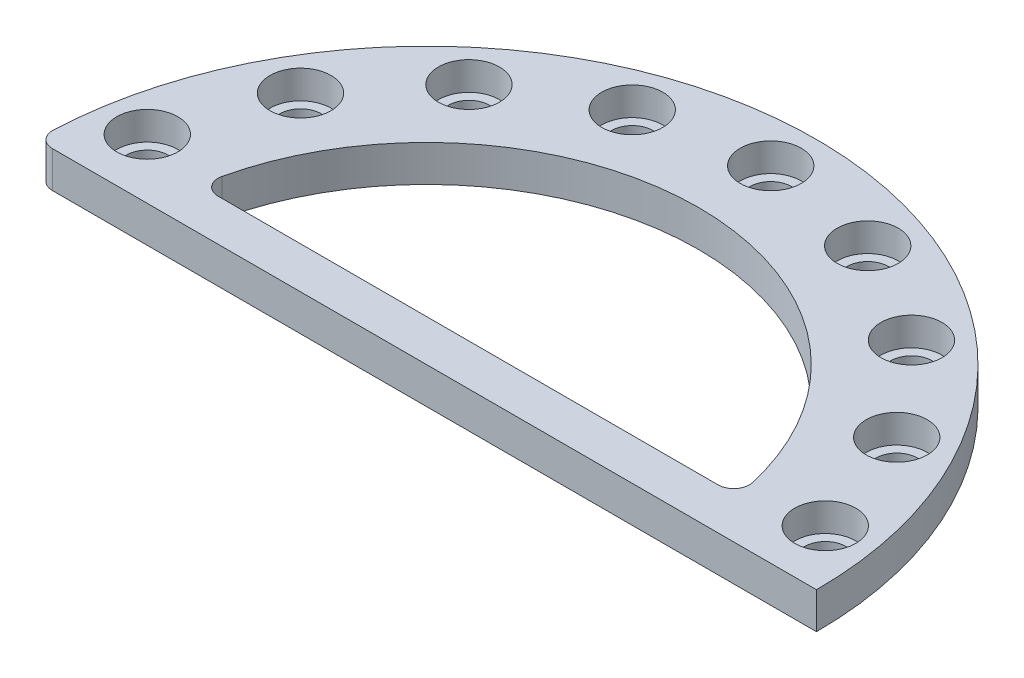
SolidWorks part; units mm, degrees
ref_plane "Front Plane" through (0, 0, 0) normal (0, 0, 1) x (1, 0, 0)
ref_plane "Top Plane" through (0, 0, 0) normal (0, 1, 0) x (1, 0, 0)
ref_plane "Right Plane" through (0, 0, 0) normal (1, 0, 0) x (0, 0, -1)
sketch "Sketch1" plane through (0, 0, 0) normal (0, 1, 0) x (1, 0, 0)
  line L0 (-51.7098, 8) -> (51.7098, 8)
  arc A0 (51.7098, 8) -> (-51.7098, 8) centre (0, 0) ccw
  circle A1 centre (0, 0) radius 75
  circle A2 centre (0, 0) radius 60.325 construction
  circle A3 centre (0, 66.2) radius 5.875 construction
  dimension "D1" = 11.75
  dimension "D2" = 8
  dimension "D3" = 120.65
  dimension "D4" = 150
  dimension "D5" = 8
extrude "Boss-Extrude1" add sketch "Sketch1" along normal blind 7
sketch "Sketch2" plane through (0, 7, 0) normal (0, 1, 0) x (1, 0, 0)
  circle A0 centre (0, 66.2) radius 5.875 construction
  circle A1 centre (0, 66.2) radius 5.875
extrude "Cut-Extrude1" cut sketch "Sketch2" against normal blind 5.45
sketch "Sketch3" plane through (0, 1.55, 0) normal (0, 1, 0) x (1, 0, 0)
  circle A0 centre (0, 66.2) radius 4
  dimension "D1" = 8
extrude "Cut-Extrude2" cut sketch "Sketch3" against normal through all
pattern_circular "CirPattern1" count 18 over 360 about axis through (0, 0, 0) along (0, 1, 0) of "Cut-Extrude1", "Cut-Extrude2"
split "Split1" trim tools "Front Plane" bodies to split 108 resulting bodies 110
fillet "Fillet1" radius 3 3 edges at (-75, 3.5, 0) (-51.7098, 3.5, -8) (51.7098, 3.5, -8)
